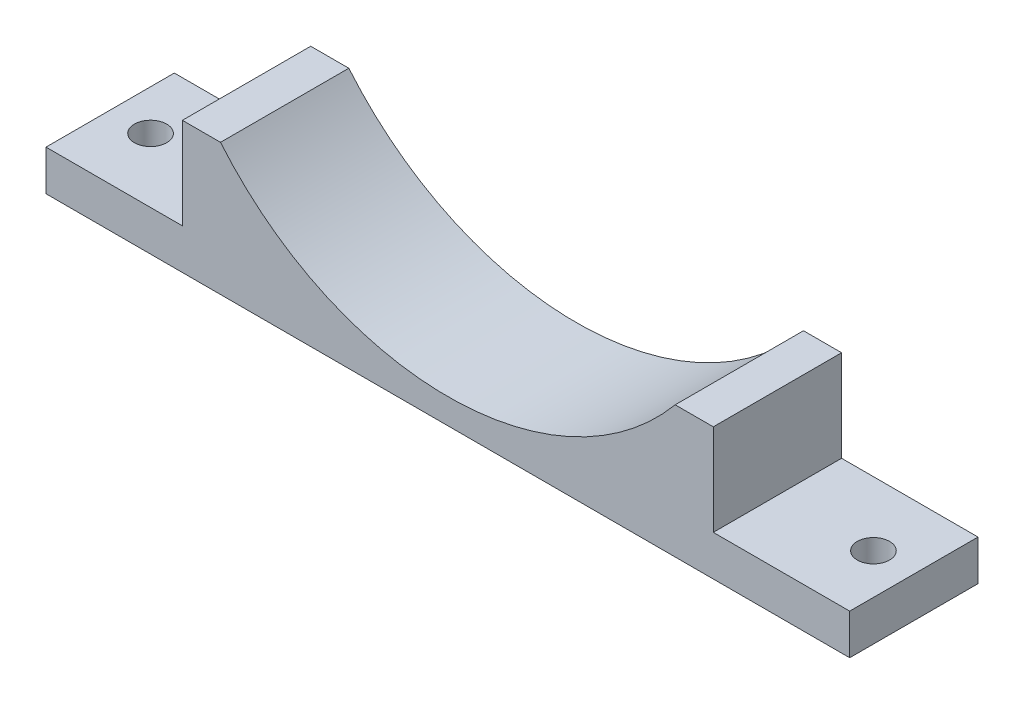
SolidWorks part; units mm, degrees
material "Custom Plastic"
ref_plane "Front Plane" through (0, 0, 0) normal (0, 0, 1) x (1, 0, 0)
ref_plane "Top Plane" through (0, 0, 0) normal (0, 1, 0) x (1, 0, 0)
ref_plane "Right Plane" through (0, 0, 0) normal (1, 0, 0) x (0, 0, -1)
sketch "Sketch1" plane through (0, 0, 0) normal (0, 0, 1) x (1, 0, 0)
  line L5 (124.545, 26.0948) -> (132.09, 26.0948)
  line L9 (132.09, 26.0948) -> (132.09, 8)
  line L10 (132.09, 8) -> (159.09, 8)
  line L11 (159.09, 8) -> (159.09, 0)
  line L12 (34.545, 26.0948) -> (27, 26.0948)
  line L13 (27, 26.0948) -> (27, 8)
  line L14 (27, 8) -> (0, 8)
  line L15 (0, 8) -> (0, 0)
  line L16 (0, 0) -> (159.09, 0)
  line L17 (21, 63.545) -> (21, 8) construction
  line L18 (34.545, 26.0948) -> (79.545, 63.545) construction
  line L19 (79.545, 63.545) -> (124.545, 26.0948) construction
  circle A1 centre (79.545, 63.545) radius 58.545 construction
  arc A2 (34.545, 26.0948) -> (124.545, 26.0948) centre (79.545, 63.545) ccw
  point P2 (21, 63.545)
  point P14 (0, 4)
  point P15 (79.545, 5)
  dimension "D1" = 90
  dimension "D4" = 58.545
  dimension "D2" = 5
  dimension "D3" = 6
  dimension "D5" = 21
  dimension "D6" = 8
extrude "Boss-Extrude1" add sketch "Sketch1" along normal blind 25.4
sketch "Sketch2" plane through (0, 8, 0) normal (0, 1, 0) x (1, 0, 0)
  line L0 (0, -25.4) -> (0, 0) construction
  line L2 (159.09, -25.4) -> (159.09, 0) construction
  circle A0 centre (8, -12.7) radius 3.2
  circle A1 centre (151.09, -12.7) radius 3.2
  point P10 (159.09, -12.7)
  dimension "D1" = 6.4
  dimension "D2" = 8
  dimension "D3" = 8
extrude "Cut-Extrude1" cut sketch "Sketch2" against normal through all
equation "\"D3@Sketch2\"=\"D2@Sketch2\""
